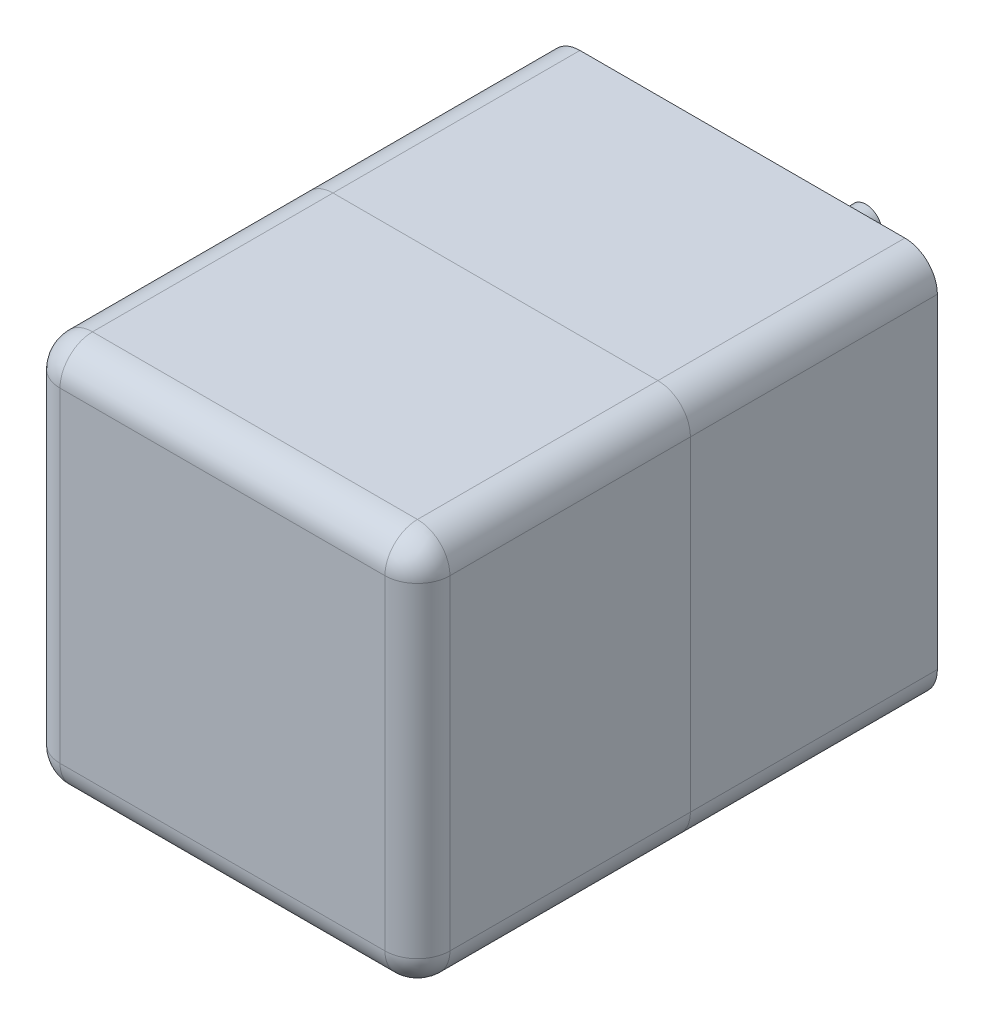
SolidWorks part; units mm, degrees
material "1023 Carbon Steel Sheet (SS)"
ref_plane "Front Plane" through (0, 0, 0) normal (0, 0, 1) x (1, 0, 0)
ref_plane "Top Plane" through (0, 0, 0) normal (0, 1, 0) x (1, 0, 0)
ref_plane "Right Plane" through (0, 0, 0) normal (1, 0, 0) x (0, 0, -1)
sketch "Sketch2" plane through (0, 0, 0) normal (0, 0, 1) x (1, 0, 0)
  line L1 (0, 0) -> (60, 0)
  line L2 (0, 0) -> (0, 60)
  line L3 (0, 60) -> (60, 60)
  line L4 (60, 0) -> (60, 60)
  dimension "D1" = 60
  dimension "D2" = 60
extrude "Boss-Extrude1" add sketch "Sketch2" along normal blind 42
sketch "Sketch3" plane through (0, 0, 0) normal (0, 0, -1) x (-1, 0, 0)
  line L4 (0, 0) -> (0, 60)
  line L5 (0, 60) -> (-60, 60)
  line L6 (-60, 60) -> (-60, 0)
  line L7 (-60, 0) -> (0, 0)
  line L8 (0, 0) -> (0, 60)
  line L9 (0, 60) -> (-60, 60)
  line L10 (-60, 60) -> (-60, 0)
  line L11 (-60, 0) -> (0, 0)
  dimension "D1" = 0
extrude "Boss-Extrude2" add sketch "Sketch3" along normal blind 38 separate body
fillet "Fillet1" radius 5 4 edges at (0, 0, 21) (60, 0, 21) (0, 60, 21) (60, 60, 21)
fillet "Fillet2" radius 5 4 edges at (0, 0, -19) (60, 0, -19) (60, 60, -19) (0, 60, -19)
fillet "Fillet3" radius 5 8 edges at (1.4645, 1.4645, 42) (0, 30, 42) (1.4645, 58.5355, 42) (30, 60, 42) (58.5355, 58.5355, 42) (60, 30, 42) (58.5355, 1.4645, 42) (30, 0, 42)
sketch "Sketch4" plane through (0, 0, -38) normal (0, 0, -1) x (-1, 0, 0)
  line L0 (-30, 60) -> (-30, 0) construction
  line L1 (-5, 60) -> (-55, 60) construction
  line L2 (-55, 0) -> (-5, 0) construction
  line L3 (-30, 30) -> (-1.4645, 58.5355) construction
  line L4 (-30, 30) -> (5, 30) construction
  circle A0 centre (-30, 30) radius 35 construction
  arc A1 (0, 55) -> (-5, 60) centre (-5, 55) ccw construction
  circle A2 centre (-5.2513, 54.7487) radius 2.25
  circle A3 centre (-54.7487, 54.7487) radius 2.25
  circle A4 centre (-54.7487, 5.2513) radius 2.25
  circle A5 centre (-5.2513, 5.2513) radius 2.25
  dimension "D1" = 70
  dimension "D2" = 4.5
extrude "Cut-Extrude1" cut sketch "Sketch4" against normal blind 10
sketch "Sketch5" plane through (0, 0, -38) normal (0, 0, -1) x (-1, 0, 0)
  line L0 (-30, 60) -> (-30, 0) construction
  line L1 (-5, 60) -> (-55, 60) construction
  line L2 (-55, 0) -> (-5, 0) construction
  line L3 (-30, 30) -> (0, 30) construction
  line L4 (0, 5) -> (0, 55) construction
  line L5 (0, 55) -> (0, 5) construction
  circle A0 centre (-30, 40) radius 12
  point P14 (-30, 28)
  point P18 (0, 30)
  dimension "D1" = 24
  dimension "D2" = 2
extrude "Boss-Extrude3" add sketch "Sketch5" along normal blind 4
sketch "Sketch6" plane through (0, 0, -42) normal (0, 0, -1) x (-1, 0, 0)
  line L0 (-30, 28) -> (-30, 40) construction
  circle A0 centre (-30, 40) radius 12 construction
  circle A1 centre (-30, 40) radius 5
  dimension "D2" = 10
  dimension "D1" = 12
extrude "Boss-Extrude4" add sketch "Sketch6" along normal blind 28 contours A1
ref_plane "Plane1" through (0, 42.5, 0) normal (0, 1, 0) x (1, 0, 0)
sketch "Sketch7" plane through (0, 42.5, 0) normal (0, 1, 0) x (1, 0, 0)
  line L0 (30, 70) -> (30, 45) construction
  line L1 (35, 70) -> (25, 70) construction
  line L2 (28, 47) -> (28, 70)
  line L3 (28, 70) -> (32, 70)
  line L4 (32, 70) -> (32, 47)
  arc A0 (28, 47) -> (32, 47) centre (30, 47) ccw
  dimension "D2" = 4
  dimension "D1" = 25
extrude "Cut-Extrude2" cut sketch "Sketch7" along normal blind 28
ref_plane "Plane2" through (30, 0, 0) normal (-1, 0, 0) x (0, 0, 1)
sketch "Sketch8" plane through (0, 0, -70) normal (0, 0, -1) x (-1, 0, 0)
  circle A0 centre (-30, 40) radius 5
extrude "Cut-Extrude3" cut sketch "Sketch8" against normal blind 33
sketch "Sketch9" plane through (0, 0, -37) normal (0, 0, -1) x (-1, 0, 0)
  circle A0 centre (-30, 40) radius 2.5
  dimension "D1" = 5
extrude "Boss-Extrude5" add sketch "Sketch9" along normal blind 20
